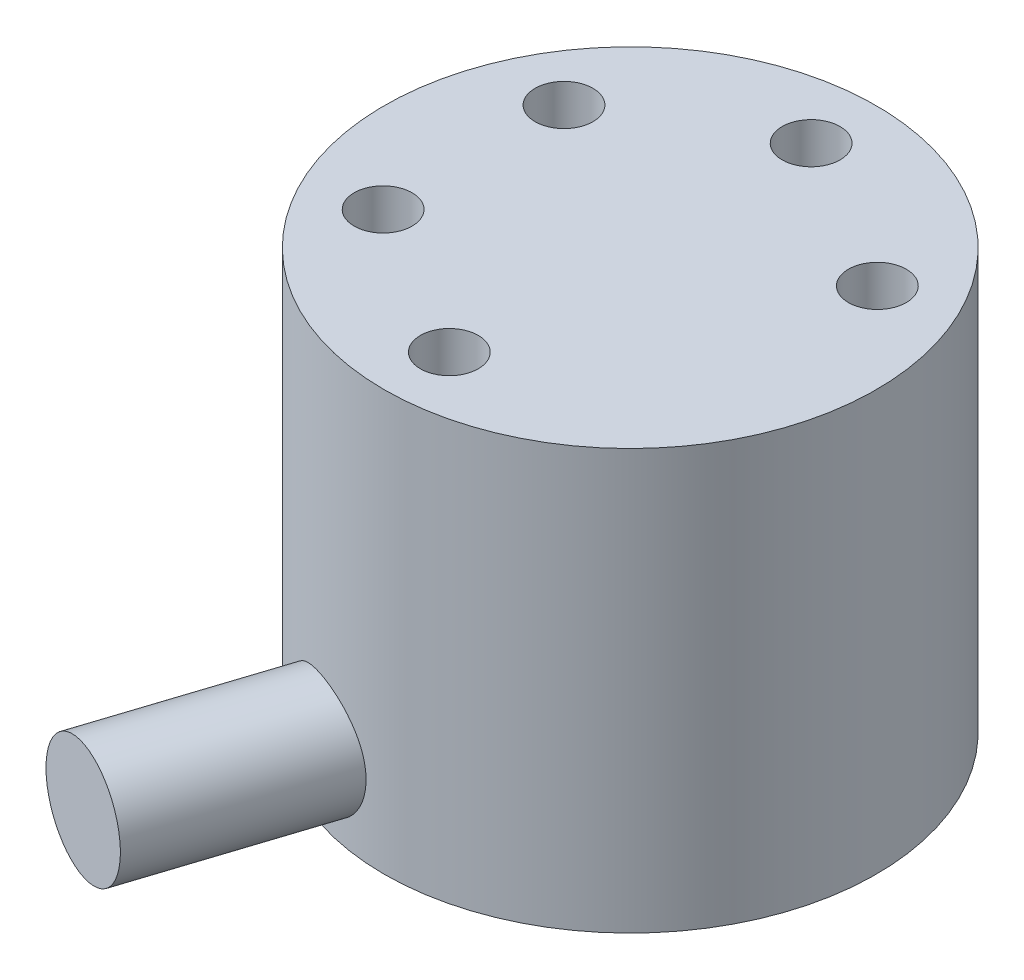
SolidWorks part; units mm, degrees
ref_plane "Front" through (0, 0, 0) normal (0, 0, 1) x (1, 0, 0)
ref_plane "Top" through (0, 0, 0) normal (0, 1, 0) x (1, 0, 0)
ref_plane "Right" through (0, 0, 0) normal (1, 0, 0) x (0, 0, -1)
ref_plane "Plane1" through (0, 0, 0) normal (0, 0, -1) x (-1, 0, 0)
sketch "Sketch1" plane through (0, 0, 0) normal (0, 0, -1) x (-1, 0, 0)
  line L0 (-8.5, 0) -> (0, 0)
  line L1 (0, 0) -> (0, 14.5)
  line L2 (0, 14.5) -> (-8.5, 14.5)
  line L3 (-8.5, 14.5) -> (-8.5, 0)
  line L4 (0, 0) -> (0, 14.5) construction
revolve "Revolve1" add sketch "Sketch1" angle 360 about L4
imported_body "Surface-Imported1"
ref_plane "Plane2" through (-8.4, 0, 0) normal (1, 0, 0) x (0, 0, -1)
sketch "Sketch2" plane through (-8.4, 0, 0) normal (1, 0, 0) x (0, 0, -1)
  line L0 (0.9, 13.234) -> (0.9, 13.2979)
  line L1 (0.9, 13.2979) -> (0.65, 13.2979)
  line L2 (0.65, 13.2979) -> (0.65, 13.5532)
  line L3 (0.65, 13.5532) -> (0.5875, 13.5532)
  line L4 (0.5875, 13.5532) -> (0.5875, 13.2979)
  line L5 (0.5875, 13.2979) -> (0.3375, 13.2979)
  line L6 (0.3375, 13.2979) -> (0.3375, 13.234)
  line L7 (0.3375, 13.234) -> (0.5875, 13.234)
  line L8 (0.5875, 13.234) -> (0.5875, 12.9787)
  line L9 (0.5875, 12.9787) -> (0.65, 12.9787)
  line L10 (0.65, 12.9787) -> (0.65, 13.234)
  line L11 (0.65, 13.234) -> (0.9, 13.234)
extrude "Cut-Extrude1" cut sketch "Sketch2" against normal up to surface
imported_body "Surface-Imported2"
ref_plane "Plane3" through (0, 0, -8.4) normal (0, 0, 1) x (1, 0, 0)
sketch "Sketch3" plane through (0, 0, -8.4) normal (0, 0, 1) x (1, 0, 0)
  line L0 (1, 13.234) -> (1, 13.2979)
  line L1 (1, 13.2979) -> (0.75, 13.2979)
  line L2 (0.75, 13.2979) -> (0.75, 13.5532)
  line L3 (0.75, 13.5532) -> (0.6875, 13.5532)
  line L4 (0.6875, 13.5532) -> (0.6875, 13.2979)
  line L5 (0.6875, 13.2979) -> (0.4375, 13.2979)
  line L6 (0.4375, 13.2979) -> (0.4375, 13.234)
  line L7 (0.4375, 13.234) -> (0.6875, 13.234)
  line L8 (0.6875, 13.234) -> (0.6875, 12.9787)
  line L9 (0.6875, 12.9787) -> (0.75, 12.9787)
  line L10 (0.75, 12.9787) -> (0.75, 13.234)
  line L11 (0.75, 13.234) -> (1, 13.234)
extrude "Cut-Extrude2" cut sketch "Sketch3" against normal up to surface
imported_body "Surface-Imported3"
sketch "Sketch4" plane through (0, 0, -8.4) normal (0, 0, 1) x (1, 0, 0)
  line L0 (-0.875, 12.5) -> (-0.4375, 13.1064)
  line L1 (-0.4375, 13.1064) -> (0, 12.5)
  line L2 (0, 12.5) -> (0.1875, 12.5)
  line L3 (0.1875, 12.5) -> (-0.3437, 13.266)
  line L4 (-0.3437, 13.266) -> (0.1875, 14)
  line L5 (0.1875, 14) -> (0, 14)
  line L6 (0, 14) -> (-0.4375, 13.3936)
  line L7 (-0.4375, 13.3936) -> (-0.875, 14)
  line L8 (-0.875, 14) -> (-1.0625, 14)
  line L9 (-1.0625, 14) -> (-0.5313, 13.266)
  line L10 (-0.5313, 13.266) -> (-1.0625, 12.5)
  line L11 (-1.0625, 12.5) -> (-0.875, 12.5)
extrude "Cut-Extrude3" cut sketch "Sketch4" against normal up to surface
imported_body "Surface-Imported4"
sketch "Sketch5" plane through (-8.4, 0, 0) normal (1, 0, 0) x (0, 0, -1)
  line L0 (-1.1, 14) -> (-0.6, 13.266)
  line L1 (-0.6, 13.266) -> (-0.6, 12.5)
  line L2 (-0.6, 12.5) -> (-0.4125, 12.5)
  line L3 (-0.4125, 12.5) -> (-0.4125, 13.266)
  line L4 (-0.4125, 13.266) -> (0.0875, 14)
  line L5 (0.0875, 14) -> (-0.1, 14)
  line L6 (-0.1, 14) -> (-0.5063, 13.3936)
  line L7 (-0.5063, 13.3936) -> (-0.9125, 14)
  line L8 (-0.9125, 14) -> (-1.1, 14)
extrude "Cut-Extrude4" cut sketch "Sketch5" against normal up to surface
ref_plane "Plane4" through (0, 2.49, 0) normal (0, 1, 0) x (1, 0, 0)
sketch "Sketch6" plane through (0, 2.49, 0) normal (0, 1, 0) x (1, 0, 0)
  line L0 (-6.5374, -13.6478) -> (-4.6353, -14.2658)
  line L1 (-4.6353, -14.2658) -> (-2.5529, -7.857)
  line L2 (-2.5529, -7.857) -> (-4.455, -7.239)
  line L3 (-4.455, -7.239) -> (-6.5374, -13.6478)
  line L4 (-4.6353, -14.2658) -> (-2.5529, -7.857) construction
revolve "Revolve2" add sketch "Sketch6" angle 360 about L4
hole_wizard "Ø2.0 (2) Diameter Hole1" positions "Sketch8" profile "Sketch7" hole size "Ø2.0" standard "ANSI Metric"
sketch "Sketch8" plane through (0, 0, 0) normal (0, -1, 0) x (-1, 0, 0)
  point P0 (1.0853, 6.155)
  point P1 (-5.8731, -2.1376)
sketch "Sketch7" plane through (-1.0853, 0, -6.155) normal (1, 0, 0) x (0, 0, -1)
  line L0 (0, 0) -> (0, 3)
  line L1 (0, 3) -> (1, 3)
  line L2 (1, 3) -> (1, 0)
  line L5 (1, 0) -> (0, 0)
  line L10 (0, 3) -> (-1, 3) construction
  line L11 (0, -6.35) -> (0, 107.95) construction
  dimension "Hole Dia." = 2
  dimension "Hole Depth" = 3
  dimension "Drill Angle" = 180
hole_wizard "Ø2.0 (2) Diameter Hole2" positions "Sketch10" profile "Sketch9" hole size "Ø2.0" standard "ANSI Metric"
sketch "Sketch10" plane through (0, 0, 0) normal (0, -1, 0) x (-1, 0, 0)
  point P0 (6.2262, -0.5447)
  point P1 (-3.5849, -5.1197)
  point P2 (-2.6414, 5.6644)
sketch "Sketch9" plane through (-6.2262, 0, 0.5447) normal (1, 0, 0) x (0, 0, -1)
  line L0 (0, 0) -> (0, 3.5)
  line L1 (0, 3.5) -> (1, 3.5)
  line L2 (1, 3.5) -> (1, 0)
  line L5 (1, 0) -> (0, 0)
  line L10 (0, 3.5) -> (-1, 3.5) construction
  line L11 (0, -6.35) -> (0, 107.95) construction
  dimension "Hole Dia." = 2
  dimension "Hole Depth" = 3.5
  dimension "Drill Angle" = 180
hole_wizard "Ø2.0 (2) Diameter Hole3" positions "Sketch12" profile "Sketch11" hole size "Ø2.0" standard "ANSI Metric"
sketch "Sketch12" plane through (0, 14.5, 0) normal (0, 1, 0) x (1, 0, 0)
  point P0 (0, 6.25)
  point P1 (-5.4127, -3.125)
sketch "Sketch11" plane through (0, 14.5, -6.25) normal (1, 0, 0) x (0, 0, 1)
  line L0 (0, 0) -> (0, 3)
  line L1 (0, 3) -> (1, 3)
  line L2 (1, 3) -> (1, 0)
  line L5 (1, 0) -> (0, 0)
  line L10 (0, 3) -> (-1, 3) construction
  line L11 (0, -6.35) -> (0, 107.95) construction
  dimension "Hole Dia." = 2
  dimension "Hole Depth" = 3
  dimension "Drill Angle" = 180
hole_wizard "Ø2.0 (2) Diameter Hole4" positions "Sketch14" profile "Sketch13" hole size "Ø2.0" standard "ANSI Metric"
sketch "Sketch14" plane through (0, 14.5, 0) normal (0, 1, 0) x (1, 0, 0)
  point P0 (0, -6.25)
  point P1 (5.4127, 3.125)
  point P2 (-5.4127, 3.125)
sketch "Sketch13" plane through (0, 14.5, 6.25) normal (1, 0, 0) x (0, 0, 1)
  line L0 (0, 0) -> (0, 3.5)
  line L1 (0, 3.5) -> (1, 3.5)
  line L2 (1, 3.5) -> (1, 0)
  line L5 (1, 0) -> (0, 0)
  line L10 (0, 3.5) -> (-1, 3.5) construction
  line L11 (0, -6.35) -> (0, 107.95) construction
  dimension "Hole Dia." = 2
  dimension "Hole Depth" = 3.5
  dimension "Drill Angle" = 180
